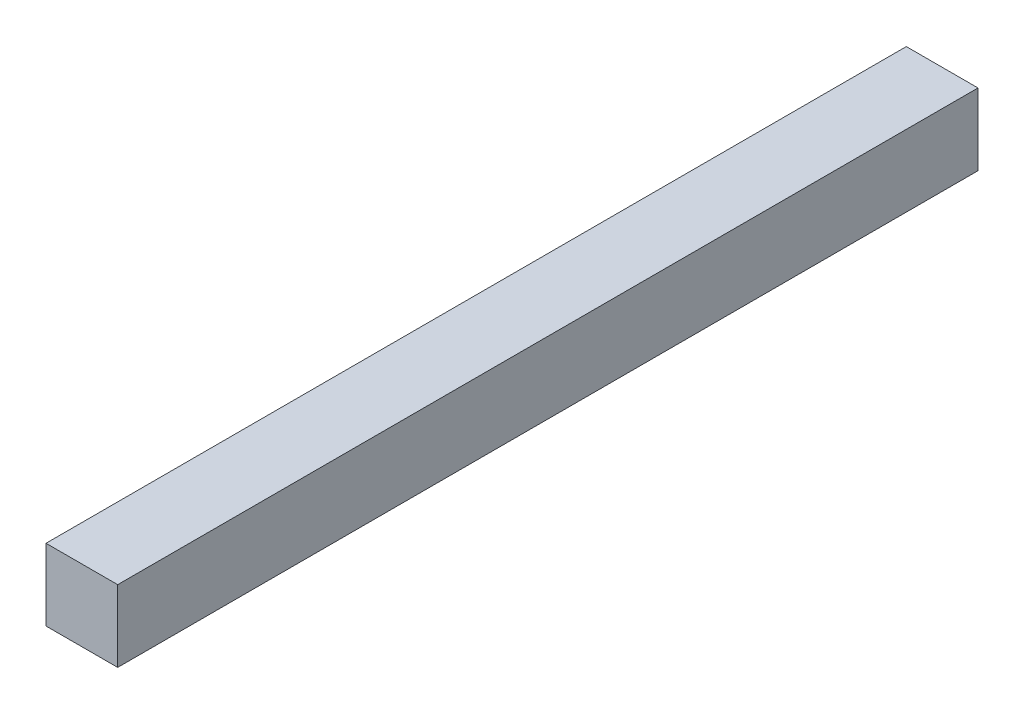
SolidWorks part; units mm, degrees
ref_plane "Plano frontal" through (0, 0, 0) normal (0, 0, 1) x (1, 0, 0)
ref_plane "Plano superior" through (0, 0, 0) normal (0, 1, 0) x (1, 0, 0)
ref_plane "Plano direito" through (0, 0, 0) normal (1, 0, 0) x (0, 0, -1)
sketch "Esboço1" plane through (0, 0, 0) normal (0, 0, 1) x (1, 0, 0)
  line L1 (-143.2855, 61.1538) -> (-93.2855, 61.1538)
  line L2 (-143.2855, 61.1538) -> (-143.2855, 11.1538)
  line L3 (-143.2855, 11.1538) -> (-93.2855, 11.1538)
  line L4 (-93.2855, 61.1538) -> (-93.2855, 11.1538)
  dimension "D1" = 50
  dimension "D2" = 50
extrude "Ressalto-extrusão1" add sketch "Esboço1" along normal blind 600 contours L2 L3 L4 L1
